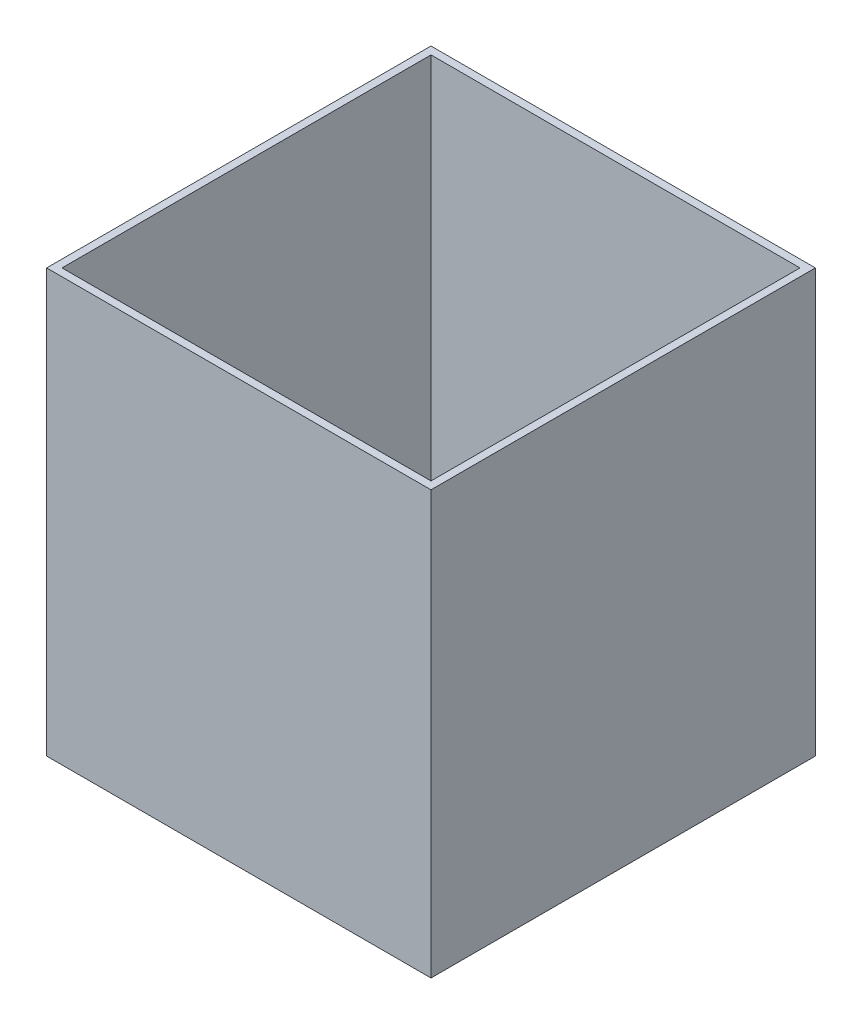
SolidWorks part; units mm, degrees
ref_plane "Płaszczyzna przednia" through (0, 0, 0) normal (0, 0, 1) x (1, 0, 0)
ref_plane "Płaszczyzna górna" through (0, 0, 0) normal (0, 1, 0) x (1, 0, 0)
ref_plane "Płaszczyzna prawa" through (0, 0, 0) normal (1, 0, 0) x (0, 0, -1)
sketch "Szkic1" plane through (0, 0, 0) normal (0, 1, 0) x (1, 0, 0)
  line L1 (-10, -10) -> (10, -10)
  line L2 (-10, -10) -> (-10, 10)
  line L3 (-10, 10) -> (10, 10)
  line L4 (10, -10) -> (10, 10)
  line L5 (-10, -10) -> (10, 10) construction
  line L6 (-10, 10) -> (10, -10) construction
  point P0 (0, 0)
  dimension "D1" = 20
extrude "Dodanie-wyciągnięcie1" add sketch "Szkic1" along normal blind 2
sketch "Szkic2" plane through (0, 2, 0) normal (0, 1, 0) x (1, 0, 0)
  line L4 (10, -10) -> (10, 10)
  line L5 (10, 10) -> (-10, 10)
  line L6 (-10, 10) -> (-10, -10)
  line L7 (-10, -10) -> (10, -10)
  line L8 (10, -10) -> (10, 10)
  line L9 (10, 10) -> (-10, 10)
  line L10 (-10, 10) -> (-10, -10)
  line L11 (-10, -10) -> (10, -10)
  dimension "D1" = 0
extrude "Wyciągnięcie-cienka ścianka1" add sketch "Szkic2" along normal blind 20 thin thin type one direction reverse wall 0.4
